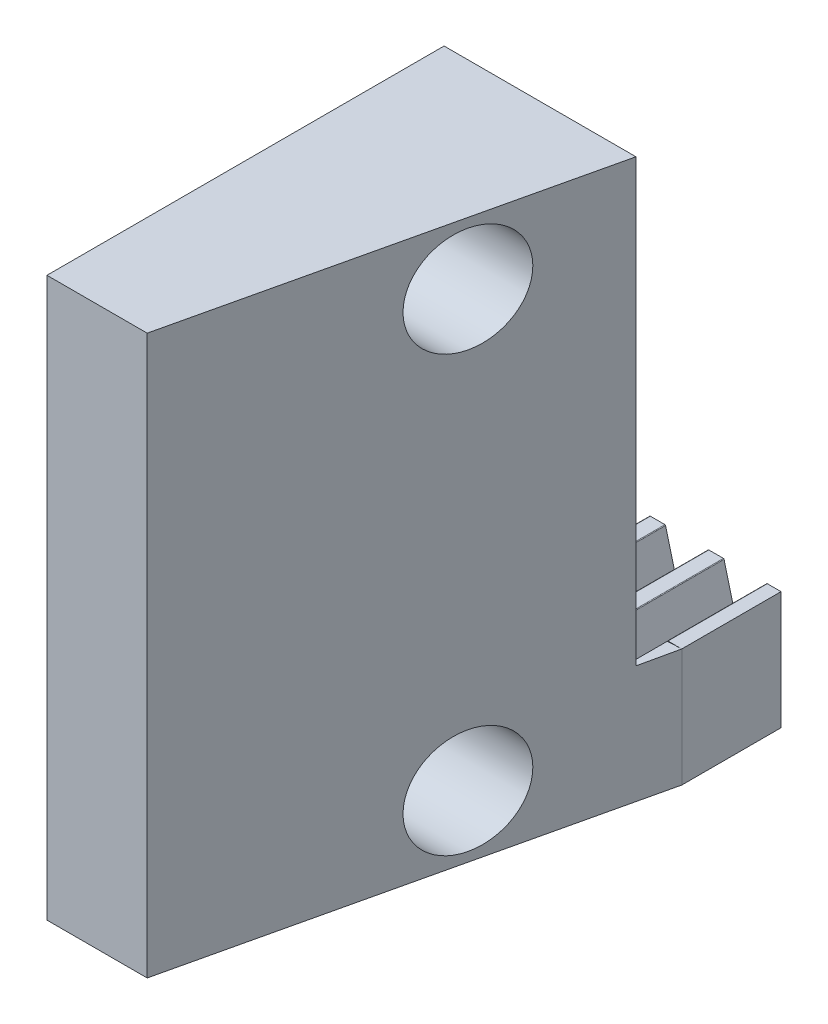
SolidWorks part; units mm, degrees
extrude "Blank" add sketch "BlankSke" against normal blind 8
sketch "BlankSke" plane through (0, 0, 0) normal (0, 0, 1) x (1, 0, 0)
  line L1 (0, 0) -> (50, 0)
  line L2 (0, 0) -> (0, 9.5)
  line L3 (0, 9.5) -> (50, 9.5)
  line L4 (50, 0) -> (50, 9.5)
  dimension "Length" = 50
  dimension "Blank_height" = 9.5
ref_plane "Plane1" through (0, 0, 0) normal (0, 0, 1) x (1, 0, 0)
ref_plane "Plane2" through (0, 0, 0) normal (0, 1, 0) x (1, 0, 0)
ref_plane "Plane3" through (0, 0, 0) normal (1, 0, 0) x (0, 0, -1)
other "Configuration Table"
sketch "HoldingSke" plane through (0, 0, 0) normal (0, 1, 0) x (1, 0, 0)
  line L0 (0, 0) -> (0.0928, 0.6602)
  line L1 (-15, 0) -> (100, 0) construction
  line L2 (0, 0) -> (-2.1039, 2.3779)
  line L3 (0, 0) -> (-11.863, 4.5341)
  line L4 (0, 0) -> (8.4473, 1.7955)
  line L5 (0, 0) -> (-23.7986, -8.8762)
  line L6 (0, 0) -> (-10.5278, -7.1032)
  line L9 (-67.7845, 28.3722) -> (-19.3772, 40.8912)
  line L10 (-76.2, 3.8779) -> (-68.2, 3.8779)
  line L11 (0, 0) -> (-8, 0)
  line L12 (-76.2, 101.6) -> (-76.147, 101.6)
  line L13 (24.9733, 27.94) -> (52.9518, 28.4284)
  line L14 (24.9733, 27.94) -> (24.9743, 27.94)
  line L15 (24.9733, 27.94) -> (100.4006, 29.5858)
  circle A0 centre (0, 0) radius 19.05
  circle A1 centre (0, 0) radius 4
  circle A2 centre (0, 0) radius 12.7
  dimension "MPH" = 8
  dimension "Diameter" = 38.1
  dimension "Num_teeth" = 12
  dimension "Pitch" = 0.6667
  dimension "Show_teeth" = 998
  dimension "Thickness" = 12.7
  dimension "Ap" = 14.5
  dimension "Pitch_height" = 8
  dimension "Width" = 8
  dimension "Backlash" = 0.053
  dimension "Addendum_fac" = 1
  dimension "Dedendum_fac" = 1.25
  dimension "Clearance_fac" = 0.25
  dimension "Dedendum_add" = 0.001
  dimension "Length" = 50
  dimension "Module" = 1.5
sketch "TooCutSkeIll" plane through (0, 0, 0) normal (0, 0, 1) x (1, 0, 0)
  line L0 (-1.7134, 9.455) -> (-0.9251, 6.4069)
  line L1 (-0.5611, 6.125) -> (0.5611, 6.125)
  line L2 (0.9251, 6.4069) -> (1.7134, 9.455)
  line L3 (50, 9.5) -> (0, 9.5) construction
  line L4 (0, 0) -> (0, 64.897) construction
  line L5 (-13.208, 8) -> (12.954, 8) construction
  line L6 (0, 0) -> (50, 0) construction
  line L7 (1.3371, 8) -> (1.3371, 48.7463) construction
  line L8 (-1.3371, 8) -> (-1.3371, 48.7463) construction
  line L9 (1.7715, 9.5) -> (1.7715, 9.5254)
  line L10 (-1.7715, 9.5) -> (-1.7715, 9.5254)
  line L11 (-1.7715, 9.5254) -> (1.7715, 9.5254)
  arc A0 (0.5611, 6.125) -> (0.9251, 6.4069) centre (0.5611, 6.501) ccw
  arc A1 (-0.9251, 6.4069) -> (-0.5611, 6.125) centre (-0.5611, 6.501) ccw
  arc A2 (1.7715, 9.5) -> (1.7134, 9.455) centre (1.7715, 9.44) ccw
  arc A3 (-1.7134, 9.455) -> (-1.7715, 9.5) centre (-1.7715, 9.44) ccw
  dimension "Pitch_height" = 8
  dimension "Addendum_plus" = 1.5254
  dimension "Pressure_angle" = 14.5
  dimension "Gap_width" = 2.6742
  dimension "Dedendum" = 1.875
extrude "ToothCutIll" cut sketch "TooCutSkeIll" against normal through all
sketch "TooCutSkeSim" plane through (0, 0, 0) normal (0, 0, 1) x (1, 0, 0)
  line L0 (0.8522, 6.125) -> (-0.8522, 6.125)
  line L1 (1.7316, 9.5254) -> (0.8522, 6.125)
  line L2 (0, 17.4625) -> (0, 53.467) construction
  line L3 (1.7316, 9.5254) -> (-1.7316, 9.5254)
  line L6 (-1.7316, 9.5254) -> (-0.8522, 6.125)
  line L9 (-1.3371, 8) -> (1.3371, 8) construction
  line L10 (0, 0) -> (50, 0) construction
  line L11 (1.3371, 8) -> (1.3371, 53.467) construction
  line L12 (-1.3371, 8) -> (-1.3371, 53.467) construction
  dimension "Pitch_height" = 8
  dimension "Addendum_plus" = 1.5254
  dimension "Pressure_angle" = 14.5
  dimension "Gap_width" = 2.6742
  dimension "Dedendum" = 1.875
extrude "ToothCutSim" cut sketch "TooCutSkeSim" against normal through all
pattern_linear "TeethCuts" count 11 spacing 4.7124 along (1, 0, 0) of "ToothCutIll", "ToothCutSim"
sketch "Sketch3" plane through (50, 0, 0) normal (1, 0, 0) x (0, 0, -1)
  line L1 (0, 9.5) -> (8, 9.5)
  line L2 (0, 9.5) -> (0, 0)
  line L3 (0, 0) -> (8, 0)
  line L4 (8, 9.5) -> (8, 0)
extrude "Boss-Extrude2" [suppressed] add sketch "Sketch3" along normal blind 15
sketch "Sketch5" [suppressed] plane through (0, 9.5, 0) normal (0, 1, 0) x (1, 0, 0)
  line L1 (39.4241, 8) -> (55, 8)
  line L2 (39.4241, 8) -> (39.4241, 0)
  line L3 (39.4241, 0) -> (55, 0)
  line L4 (55, 8) -> (55, 0)
extrude "Boss-Extrude3" [suppressed] add sketch "Sketch5" along normal blind 30
sketch "Sketch7" [suppressed] plane through (0, 0, 0) normal (0, 1, 0) x (1, 0, 0)
  line L4 (65, 0) -> (39.4241, 0)
  line L5 (0, 0) -> (65, 0) construction
  line L9 (39.4241, 0) -> (39.4241, -25)
  line L10 (39.4241, -25) -> (47.2121, -25)
  line L11 (47.2121, -25) -> (65, 0)
extrude "Boss-Extrude5" [suppressed] add sketch "Sketch7" along normal blind 39.5
sketch "Sketch8" [suppressed] plane through (0, 0, -8) normal (0, 0, -1) x (-1, 0, 0)
  line L1 (-39.4241, 9.5) -> (-55, 9.5)
  line L2 (-39.4241, 9.5) -> (-39.4241, 39.5)
  line L3 (-39.4241, 39.5) -> (-55, 39.5)
  line L4 (-55, 9.5) -> (-55, 39.5)
extrude "Cut-Extrude1" [suppressed] cut sketch "Sketch8" against normal blind 11
sketch "Sketch9" [suppressed] plane through (0, 0, 25) normal (0, 0, 1) x (1, 0, 0)
  line L1 (39.4241, 39.5) -> (65, 39.5)
  line L2 (39.4241, 39.5) -> (39.4241, 0)
  line L3 (39.4241, 0) -> (65, 0)
  line L4 (65, 39.5) -> (65, 0)
extrude "Cut-Extrude2" [suppressed] cut sketch "Sketch9" against normal blind 25
sketch "Sketch10" [suppressed] plane through (0, 9.5, 0) normal (0, 1, 0) x (1, 0, 0)
  line L1 (65, 0) -> (48.8489, 0)
  line L2 (65, 0) -> (65, 8)
  line L3 (65, 8) -> (48.8489, 8)
  line L4 (48.8489, 0) -> (48.8489, 8)
extrude "Boss-Extrude6" [suppressed] add sketch "Sketch10" along normal blind 35.5
sketch "Sketch12" [suppressed] plane through (0, 45, 0) normal (0, 1, 0) x (1, 0, 0)
  line L0 (48.8489, 0) -> (65, 0)
  line L1 (48.8489, 0) -> (48.8489, -25)
  line L2 (48.8489, -25) -> (56.9245, -25)
  line L3 (56.9245, -25) -> (65, 0)
extrude "Boss-Extrude7" [suppressed] add sketch "Sketch12" against normal blind 45
sketch "Sketch13" [suppressed] plane through (0, 0, -8) normal (0, 0, -1) x (-1, 0, 0)
  line L1 (-48.8489, 9.5) -> (-65, 9.5)
  line L2 (-48.8489, 9.5) -> (-48.8489, 45)
  line L3 (-48.8489, 45) -> (-65, 45)
  line L4 (-65, 9.5) -> (-65, 45)
extrude "Cut-Extrude3" [suppressed] cut sketch "Sketch13" against normal blind 11
sketch "Sketch14" [suppressed] plane through (48.8489, 0, 0) normal (-1, 0, 0) x (0, 0, 1)
  line L1 (-8, 45) -> (25, 45) construction
  line L2 (0, 0) -> (25, 0) construction
  circle A0 centre (14, 40) radius 1.75
  circle A1 centre (14, 5) radius 1.75
  dimension "D2" = 5
  dimension "D1" = 5
extrude "Cut-Extrude4" [suppressed] cut sketch "Sketch14" against normal blind 21
sketch "Sketch16" plane through (0, 0, 0) normal (0, -1, 0) x (1, 0, 0)
  line L0 (50, 0) -> (33.849, 0)
  line L1 (0, 0) -> (50, 0) construction
  line L2 (33.849, 0) -> (33.849, 35)
  line L3 (33.849, 35) -> (41.925, 35)
  line L4 (41.925, 35) -> (50, 0)
extrude "Boss-Extrude8" add sketch "Sketch16" against normal blind 45
sketch "Sketch17" plane through (0, 0, 0) normal (0, 0, -1) x (-1, 0, 0)
  line L0 (-50, 9.5) -> (-48.8373, 9.455)
  line L1 (-48.8373, 9.455) -> (-47.9761, 6.125)
  line L2 (-47.9761, 6.125) -> (-46.2717, 6.125)
  line L3 (-46.2717, 6.125) -> (-45.4105, 9.455)
  line L4 (-45.4105, 9.455) -> (-44.1249, 9.455)
  line L5 (-44.1249, 9.455) -> (-43.2637, 6.125)
  line L6 (-43.2637, 6.125) -> (-41.5593, 6.125)
  line L7 (-41.5593, 6.125) -> (-40.6981, 9.455)
  line L8 (-40.6981, 9.455) -> (-39.4125, 9.455)
  line L9 (-39.4125, 9.455) -> (-38.5513, 6.125)
  line L10 (-38.5513, 6.125) -> (-36.8469, 6.125)
  line L11 (-36.8469, 6.125) -> (-35.9857, 9.455)
  line L12 (-35.9857, 9.455) -> (-34.7001, 9.455)
  line L13 (-34.7001, 9.455) -> (-33.8389, 6.125)
  line L14 (-33.8389, 6.125) -> (-33.849, 45)
  line L15 (-33.849, 45) -> (-50, 45)
  line L16 (-50, 45) -> (-50, 9.5)
extrude "Cut-Extrude5" cut sketch "Sketch17" against normal blind 3
sketch "Sketch20" plane through (33.849, 0, 0) normal (-1, 0, 0) x (0, 0, 1)
  line L0 (35, 45) -> (3, 45) construction
  line L1 (35, 0) -> (0, 0) construction
  circle A0 centre (14, 40) radius 4.25
  circle A1 centre (14, 5) radius 4.25
  dimension "D1" = 5
  dimension "D2" = 5
extrude "Cut-Extrude6" cut sketch "Sketch20" against normal blind 25
equation "' \"Module@HoldingSke\" = 6.35"
equation "' \"Num_teeth@HoldingSke\" = 12"
equation "' \"Ap@HoldingSke\" =  20"
equation "' \"Ap@HoldingSke\" = 20"
equation "' \"Width@HoldingSke\" = 0.25 * 25.4"
equation "' \"Show_teeth@HoldingSke\" = 500"
equation "' \"Backlash@HoldingSke\" = 0.009 * 25.4"
equation "' \"Addendum_fac@HoldingSke\" = 1.0"
equation "' \"Dedendum_fac@HoldingSke\" = 1.25"
equation "' \"Dedendum_add@HoldingSke\" = 0.00005 * 25.4"
equation "' \"Clearance_fac@HoldingSke\" = 0.25"
equation "' \"Pitch_height@HoldingSke\" = 1 * 25.4"
equation "' \"Length@HoldingSke\" = 4.71 * 25.4"
equation "\"Pitch@HoldingSke\" = 1 / \"Module@HoldingSke\""
equation "\"MPH@HoldingSke\" = \"Dedendum_fac@HoldingSke\" / \"Pitch@HoldingSke\" + 2 * \"Dedendum_add@HoldingSke\" + 0.002 * 25.4"
equation "\"MPH@HoldingSke\" = ((sgn( \"MPH@HoldingSke\" - \"Pitch_height@HoldingSke\")+1)*( \"MPH@HoldingSke\" - \"Pitch_height@HoldingSke\"))/2 + \"Pitch_height@HoldingSke\""
equation "\"Blank_height@BlankSke\" = \"Pitch_height@HoldingSke\" + \"Addendum_fac@HoldingSke\"  / \"Pitch@HoldingSke\" "
equation "\"Length@BlankSke\" =  \"Length@HoldingSke\""
equation "\"Face_width@Blank\" = \"Width@HoldingSke\""
equation "\"Pressure_angle@TooCutSkeIll\" = \"Ap@HoldingSke\""
equation "\"Addendum_plus@TooCutSkeIll\" =  \"Addendum_fac@HoldingSke\"  / \"Pitch@HoldingSke\" + 0.001 *25.4"
equation "\"Dedendum@TooCutSkeIll\" = \"Dedendum_fac@HoldingSke\"  / \"Pitch@HoldingSke\""
equation "\"Pitch_height@TooCutSkeIll\" =  \"MPH@HoldingSke\""
equation "\"Gap_width@TooCutSkeIll\" = 3.14159265 / 2 / \"Pitch@HoldingSke\" + 6 * \"Backlash@HoldingSke\""
equation "\"Pressure_angle@TooCutSkeSim\" = \"Ap@HoldingSke\""
equation "\"Addendum_plus@TooCutSkeSim\" =  \"Addendum_fac@HoldingSke\"  / \"Pitch@HoldingSke\" + 0.001 * 25.4"
equation "\"Dedendum@TooCutSkeSim\" = \"Dedendum_fac@HoldingSke\"  / \"Pitch@HoldingSke\""
equation "\"Pitch_height@TooCutSkeSim\" =  \"MPH@HoldingSke\""
equation "\"Gap_width@TooCutSkeSim\" = 3.14159265 / 2 / \"Pitch@HoldingSke\" + 6 * \"Backlash@HoldingSke\""
equation "\"Root_fillet@TooCutSkeIll\" = \"Clearance_fac@HoldingSke\" / \"Pitch@HoldingSke\" + \"Dedendum_add@HoldingSke\""
equation "\"Break_rad@TooCutSkeIll\" = 0.02 / \"Pitch@HoldingSke\" * 2"
equation "\"Linear_pitch@TeethCuts\" = 3.14159265 / \"Pitch@HoldingSke\""
equation "\"Num_teeth@HoldingSke\" = int( ( \"Length@HoldingSke\" + 0 ) / (3.14159265 / \"Pitch@HoldingSke\")) + 0.9999  + 1"
equation " \"Num_teeth@TeethCuts\" = int( \"Show_teeth@HoldingSke\" ) + 1"
equation " \"Num_teeth@TeethCuts\" = ((sgn( \"Num_teeth@TeethCuts\" - \"Num_teeth@HoldingSke\" )-1)*( \"Num_teeth@TeethCuts\" - \"Num_teeth@HoldingSke\" ))/-2+ \"Num_teeth@HoldingSke\""
equation " \"Num_teeth@TeethCuts\" = ((sgn( \"Num_teeth@TeethCuts\" - 2.0)+1)*( \"Num_teeth@TeethCuts\" - 2.0))/2 +2.0"
